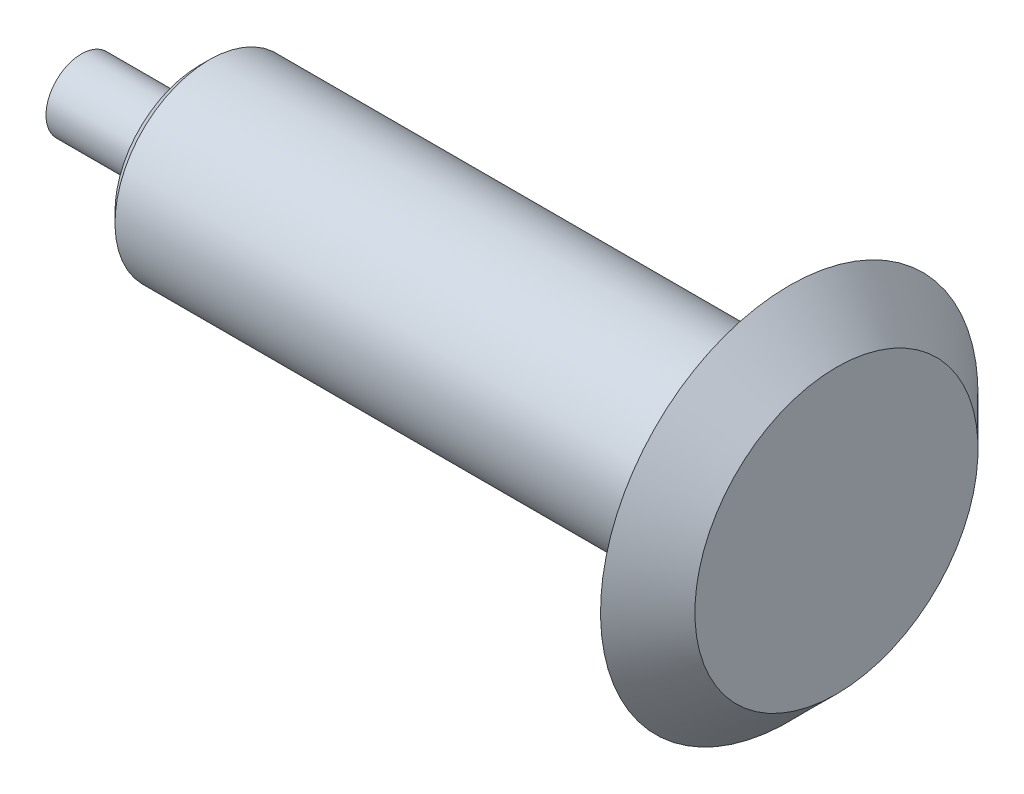
SolidWorks part; units mm, degrees
ref_plane "Alzado" through (0, 0, 0) normal (0, 0, 1) x (1, 0, 0)
ref_plane "Planta" through (0, 0, 0) normal (0, 1, 0) x (1, 0, 0)
ref_plane "Vista lateral" through (0, 0, 0) normal (1, 0, 0) x (0, 0, -1)
sketch "Croquis1" plane through (0, 0, 0) normal (0, 0, 1) x (1, 0, 0)
  line L0 (0, 0) -> (0, 7.5)
  line L1 (0, 7.5) -> (25, 7.5)
  line L9 (160, 0) -> (0, 0)
  line L10 (160, 0) -> (160, 30)
  line L11 (25, 7.5) -> (25, 17.8787)
  line L12 (25, 17.8787) -> (27.1213, 20)
  line L13 (150, 30) -> (150, 40)
  line L15 (27.1213, 20) -> (140, 20)
  line L16 (140, 20) -> (150, 30)
  line L18 (150, 40) -> (160, 30)
  dimension "D1" = 25
  dimension "D2" = 160
  dimension "D3" = 30
  dimension "D4" = 7.5
  dimension "D5" = 20
  dimension "D6" = 45
  dimension "D7" = 3
revolve "Revolución1" add sketch "Croquis1" angle 360 about L9
